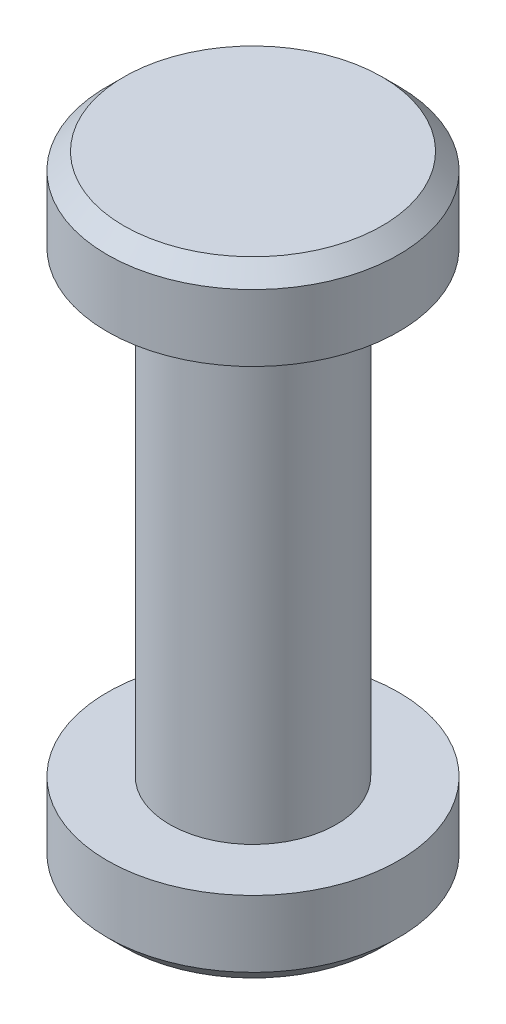
SolidWorks part; units mm, degrees
ref_plane "Front Plane" through (0, 0, 0) normal (0, 0, 1) x (1, 0, 0)
ref_plane "Top Plane" through (0, 0, 0) normal (0, 1, 0) x (1, 0, 0)
ref_plane "Right Plane" through (0, 0, 0) normal (1, 0, 0) x (0, 0, -1)
sketch "Sketch1" plane through (0, 0, 0) normal (0, 1, 0) x (1, 0, 0)
  circle A0 centre (0, 0) radius 1
  dimension "D1" = 2
extrude "Boss-Extrude1" add sketch "Sketch1" along normal blind 5.5
sketch "Sketch2" plane through (0, 5.5, 0) normal (0, 1, 0) x (1, 0, 0)
  circle A0 centre (0, 0) radius 1.75
  dimension "D1" = 3.5
extrude "Boss-Extrude2" add sketch "Sketch2" along normal blind 1
chamfer "Chamfer1" distance 0.2 angle 45 1 edges at (0, 6.5, 1.75)
sketch "Sketch3" plane through (0, 0, 0) normal (0, -1, 0) x (1, 0, 0)
  circle A0 centre (0, 0) radius 1.75
  dimension "D1" = 3.5
extrude "Boss-Extrude3" add sketch "Sketch3" along normal blind 1
chamfer "Chamfer2" distance 0.2 angle 45 1 edges at (0, -1, -1.75)
